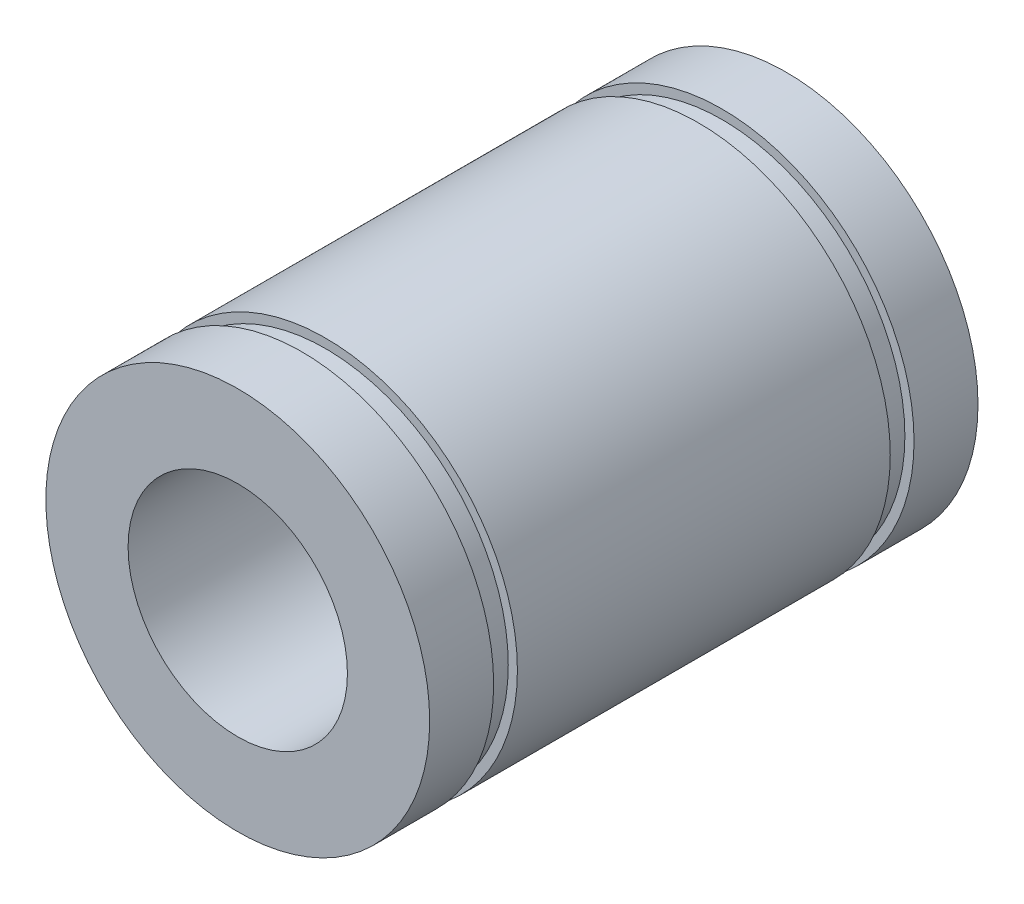
SolidWorks part; units mm, degrees
ref_plane "Front Plane" through (0, 0, 0) normal (0, 0, 1) x (1, 0, 0)
ref_plane "Top Plane" through (0, 0, 0) normal (0, 1, 0) x (1, 0, 0)
ref_plane "Right Plane" through (0, 0, 0) normal (1, 0, 0) x (0, 0, -1)
sketch "Sketch1" plane through (0, 0, 0) normal (0, 1, 0) x (1, 0, 0)
  line L0 (10.5, 0) -> (6, 0)
  line L1 (6, 0) -> (6, -30)
  line L2 (6, -30) -> (10.5, -30)
  line L3 (10.5, -30) -> (10.5, -26.5)
  line L4 (10.5, -26.5) -> (10, -26.5)
  line L5 (10, -26.5) -> (10, -25.2)
  line L6 (10, -25.2) -> (10.5, -25.2)
  line L7 (10.5, -25.2) -> (10.5, -4.8)
  line L8 (10.5, -4.8) -> (10, -4.8)
  line L9 (10, -4.8) -> (10, -3.5)
  line L10 (10, -3.5) -> (10.5, -3.5)
  line L11 (10.5, -3.5) -> (10.5, 0)
  line L12 (0, 0) -> (0, -30) construction
revolve "Revolve1" add sketch "Sketch1" angle 360 about L12
